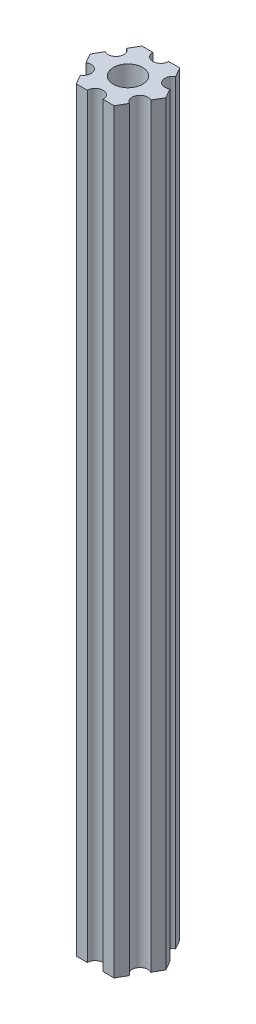
SolidWorks part; units mm, degrees
material "Churro - 6005A-T61"
ref_plane "Plano frontal" through (0, 0, 0) normal (0, 0, 1) x (1, 0, 0)
ref_plane "Plano superior" through (0, 0, 0) normal (0, 1, 0) x (1, 0, 0)
ref_plane "Plano direito" through (0, 0, 0) normal (1, 0, 0) x (0, 0, -1)
ref_plane "Plano1" through (0, 85, 0) normal (0, 1, 0) x (1, 0, 0)
sketch "Esboço1" plane through (0, 85, 0) normal (0, 1, 0) x (1, 0, 0)
  line L0 (6.1627, -1.826) -> (7.2169, 0)
  line L1 (7.2169, 0) -> (6.1627, 1.826)
  line L2 (4.6627, 4.424) -> (3.6084, 6.25)
  line L3 (3.6084, 6.25) -> (1.5, 6.25)
  line L4 (-1.5, 6.25) -> (-3.6084, 6.25)
  line L5 (-3.6084, 6.25) -> (-4.6627, 4.424)
  line L6 (-6.1627, 1.826) -> (-7.2169, 0)
  line L7 (-7.2169, 0) -> (-6.1627, -1.826)
  line L8 (-4.6627, -4.424) -> (-3.6084, -6.25)
  line L9 (-3.6084, -6.25) -> (-1.5, -6.25)
  line L10 (1.5, -6.25) -> (3.6084, -6.25)
  line L11 (3.6084, -6.25) -> (4.6627, -4.424)
  arc A0 (6.1627, 1.826) -> (4.6627, 4.424) centre (5.4127, 3.125) cw
  arc A1 (1.5, 6.25) -> (-1.5, 6.25) centre (0, 6.25) cw
  arc A2 (-4.6627, 4.424) -> (-6.1627, 1.826) centre (-5.4127, 3.125) cw
  arc A3 (-6.1627, -1.826) -> (-4.6627, -4.424) centre (-5.4127, -3.125) cw
  arc A4 (-1.5, -6.25) -> (1.5, -6.25) centre (0, -6.25) cw
  arc A5 (4.6627, -4.424) -> (6.1627, -1.826) centre (5.4127, -3.125) cw
  circle A6 centre (0, 0) radius 2.79
extrude "Ressalto-extrusão1" add sketch "Esboço1" against normal blind 144
